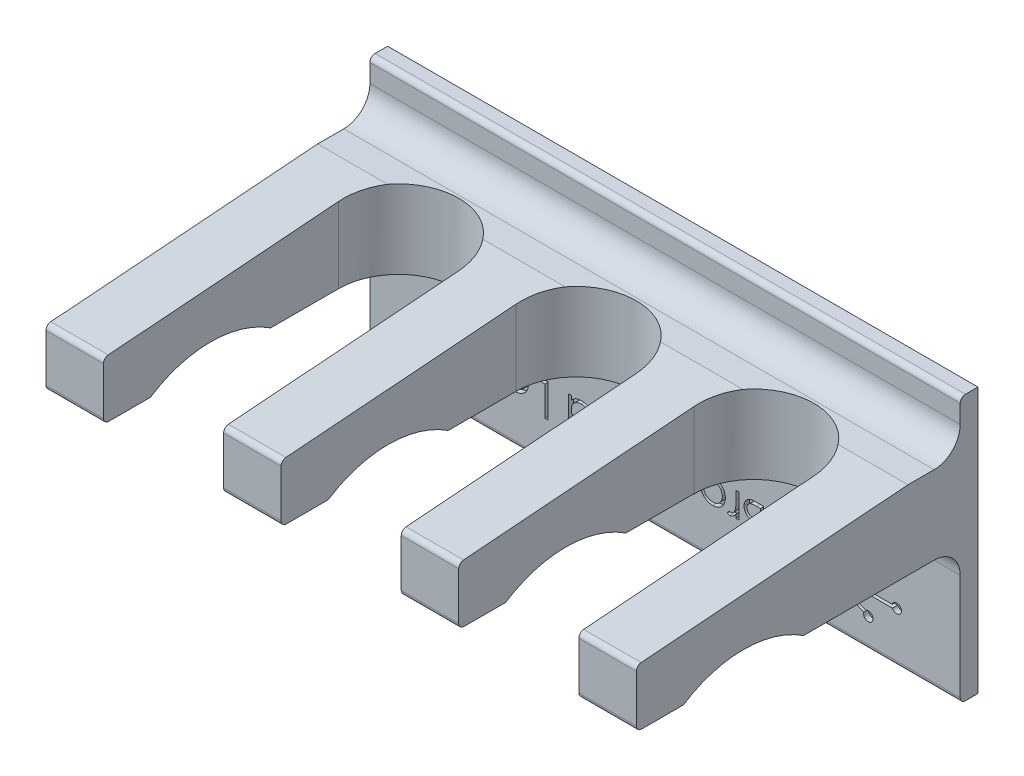
SolidWorks part; units mm, degrees
ref_plane "Front Plane" through (0, 0, 0) normal (0, 0, 1) x (1, 0, 0)
ref_plane "Top Plane" through (0, 0, 0) normal (0, 1, 0) x (1, 0, 0)
ref_plane "Right Plane" through (0, 0, 0) normal (1, 0, 0) x (0, 0, -1)
sketch "Sketch1" plane through (0, 0, 0) normal (0, 1, 0) x (1, 0, 0)
  line L5 (-56.5, 1.7) -> (56.5, 1.7)
  line L6 (-56.5, 1.7) -> (-56.5, -1.7)
  line L7 (-56.5, -1.7) -> (56.5, -1.7)
  line L8 (56.5, 1.7) -> (56.5, -1.7)
  line L9 (-56.5, 1.7) -> (56.5, -1.7) construction
  line L10 (-56.5, -1.7) -> (56.5, 1.7) construction
  point P0 (0, 0)
  dimension "D1" = 3.4
  dimension "D2" = 113
extrude "Boss-Extrude1" add sketch "Sketch1" along normal blind 30 and the other way blind 20.8
sketch "Sketch2" plane through (0, 0, 1.7) normal (0, 0, 1) x (1, 0, 0)
  line L6 (-56.5, 20.5) -> (56.5, 20.5)
  line L7 (-56.5, 20.5) -> (-56.5, 5.5)
  line L8 (-56.5, 5.5) -> (56.5, 5.5)
  line L9 (56.5, 20.5) -> (56.5, 5.5)
  line L10 (-56.5, 20.5) -> (56.5, 5.5) construction
  line L11 (-56.5, 5.5) -> (56.5, 20.5) construction
  line L12 (-56.5, 30) -> (56.5, 30) construction
  point P0 (0, 13)
  dimension "D1" = 13
  dimension "D2" = 15
extrude "Boss-Extrude2" add sketch "Sketch2" along normal blind 62
sketch "Sketch4" plane through (-56.5, 0, 0) normal (-1, 0, 0) x (0, 0, 1)
  line L0 (11.7, 20.5) -> (63.7, 20.5)
  line L1 (63.7, 20.5) -> (1.7, 20.5) construction
  line L2 (63.7, 20.5) -> (63.7, 16.5)
  line L3 (63.7, 20.5) -> (63.7, 5.5) construction
  line L4 (63.7, 16.5) -> (11.7, 20.5)
  line L5 (63.7, 5.5) -> (1.7, 5.5) construction
  arc A0 (54.7, 5.5) -> (31.7, 5.5) centre (43.2, -12.0767) ccw
  point P5 (43.2, 8.9278)
  line M3 (1.7, 5.5) -> (63.7, 5.5)
  line M4 (63.7, 5.5) -> (63.7, 20.5)
  line M5 (63.7, 20.5) -> (1.7, 20.5)
  dimension "D1" = 23
  dimension "D2" = 9
  dimension "D3" = 11
  dimension "D4" = 12
  dimension "D5" = 10
extrude "Cut-Extrude1" cut sketch "Sketch4" against normal through all and the other way through all contours A0 M3 | L4 M4 M5
sketch "Sketch5" plane through (0, 5.5, 1.0307) normal (0, 1, 0) x (1, 0, 0)
  line L0 (-45.5, -62.6693) -> (-45.5, -17.6693)
  line L1 (56.5, -62.6693) -> (-56.5, -62.6693) construction
  line L2 (-45.5, -17.6693) -> (-22.5, -17.6693)
  line L3 (-22.5, -17.6693) -> (-22.5, -62.6693)
  line L4 (-22.5, -62.6693) -> (-45.5, -62.6693)
  line L5 (-11.5, -62.6693) -> (-11.5, -17.6693)
  line L6 (-11.5, -17.6693) -> (11.5, -17.6693)
  line L7 (11.5, -17.6693) -> (11.5, -62.6693)
  line L8 (11.5, -62.6693) -> (-11.5, -62.6693)
  line L9 (22.5, -62.6693) -> (22.5, -17.6693)
  line L10 (22.5, -17.6693) -> (45.5, -17.6693)
  line L11 (45.5, -17.6693) -> (45.5, -62.6693)
  line L12 (45.5, -62.6693) -> (22.5, -62.6693)
  arc A0 (-45.5, -17.6693) -> (-22.5, -17.6693) centre (-34, -17.6693) cw
  arc A1 (-11.5, -17.6693) -> (11.5, -17.6693) centre (0, -17.6693) cw
  arc A2 (22.5, -17.6693) -> (45.5, -17.6693) centre (34, -17.6693) cw
  line M24 (56.5, -30.6693) -> (-56.5, -30.6693)
  dimension "D1" = 11
  dimension "D2" = 23
  dimension "D4" = 45
  dimension "D5" = 11
  dimension "D3" = 3
extrude "Cut-Extrude5" cut sketch "Sketch5" against normal through all both and the other way through all contours L10 L11 L9 M24 | L11 L12 L9 M24 | L10 A2 | L6 A1 | L6 L7 L5 M24 | L7 L8 L5 M24 | L2 L3 L0 M24 | L3 L4 L0 M24 | L2 A0
fillet "Fillet1" radius 5 2 edges at (0, 20.5, 1.7) (0, 5.5, 1.7)
fillet "Fillet2" radius 1 2 edges at (0, -20.8, 1.7) (0, 30, 1.7)
fillet "Fillet3" radius 1 8 edges at (-51, 5.5, 63.7) (51, 5.5, 63.7) (-51, 16.5, 63.7) (51, 16.5, 63.7) (-17, 5.5, 63.7) (-17, 16.5, 63.7) (17, 5.5, 63.7) (17, 16.5, 63.7)
sketch "Sketch6" plane through (0, 0, 1.7) normal (0, 0, 1) x (1, 0, 0)
  line L0 (31.204, -8.882) -> (34.2634, -3.8987)
  line L1 (34.7685, -4.2226) -> (31.7247, -9.1807)
  line L2 (40.6007, -5.2917) -> (32.0081, -9.4414)
  line L3 (40.937, -5.7955) -> (32.3521, -9.9415)
  line L4 (32.5852, -10.8401) -> (43.4687, -10.8401)
  line L5 (43.5228, -11.4401) -> (32.5287, -11.4401)
  line L6 (32.3874, -11.8534) -> (38.4197, -14.3433)
  line L7 (38.0395, -14.8355) -> (32.0607, -12.3677)
  line L8 (30.3451, -8.7203) -> (30.3451, -13.1484)
  arc A1 (34.7685, -4.2226) -> (34.2634, -3.8987) centre (34.974, -3.3464) ccw
  arc A2 (40.937, -5.7955) -> (40.6007, -5.2917) centre (41.4737, -5.0731) ccw
  arc A3 (43.5228, -11.4401) -> (43.4687, -10.8401) centre (44.3404, -11.0638) ccw
  arc A4 (38.0395, -14.8355) -> (38.4197, -14.3433) centre (38.898, -15.1058) ccw
  arc A5 (30.3451, -13.1484) -> (30.3451, -8.7203) centre (30.373, -10.9344) ccw
  dimension "D1" = 0.9
  dimension "D2" = 0.6
  dimension "D3" = 0.6
  dimension "D4" = 0.6
  dimension "D5" = 0.6
sketch "Sketch7" plane through (0, 0, 1.7) normal (0, 0, 1) x (1, 0, 0)
  line L0 (-56.5, -6.8968) -> (19.6724, -6.8968)
  point P4 (19.6724, -9.65)
sketch "Sketch8" plane through (0, 0, 1.7) normal (0, 0, 1) x (1, 0, 0)
  text T0 "Brouhard Lab" font "Century Gothic" height in points 24
extrude "Cut-Extrude6" cut sketch "Sketch6" against normal blind 1 contours A5 L8 | A5 L7 A4 L6 | A5 L5 A3 L4 | A5 L3 A2 L2 | A5 L1 A1 L0
extrude "Cut-Extrude7" cut sketch "Sketch8" against normal blind 1
